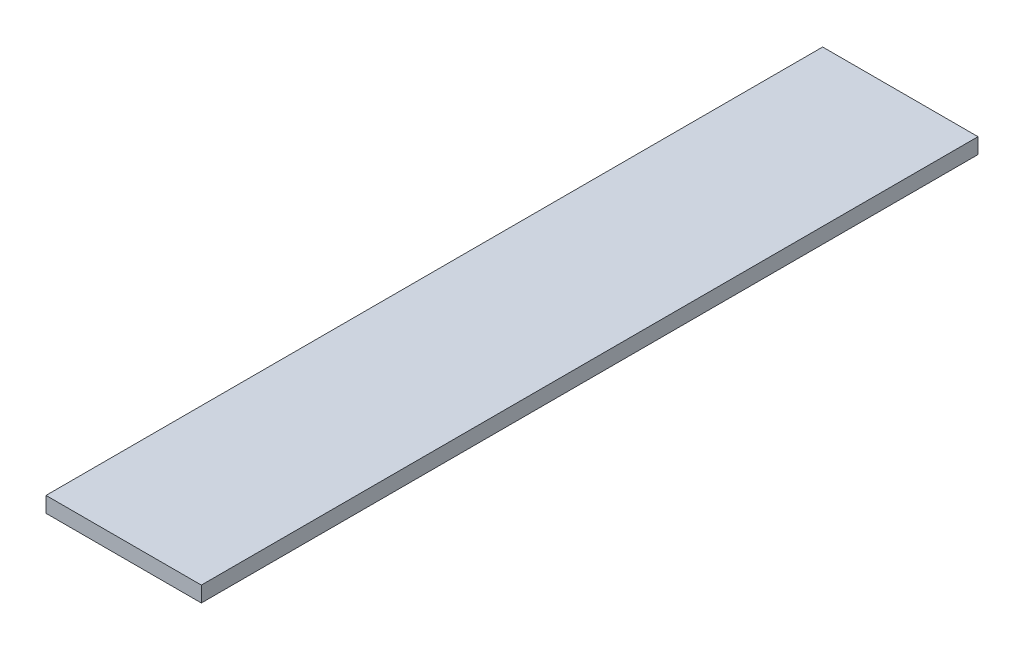
SolidWorks part; units mm, degrees
ref_plane "Front Plane" through (0, 0, 0) normal (0, 0, 1) x (1, 0, 0)
ref_plane "Top Plane" through (0, 0, 0) normal (0, 1, 0) x (1, 0, 0)
ref_plane "Right Plane" through (0, 0, 0) normal (1, 0, 0) x (0, 0, -1)
sketch "Sketch1" plane through (0, 0, 0) normal (0, 0, 1) x (1, 0, 0)
  line L1 (0, 0) -> (20000, 0)
  line L2 (0, 0) -> (0, -2000)
  line L3 (0, -2000) -> (20000, -2000)
  line L4 (20000, 0) -> (20000, -2000)
  dimension "D1" = 2000
  dimension "D2" = 20000
extrude "Boss-Extrude1" add sketch "Sketch1" along normal blind 100000
